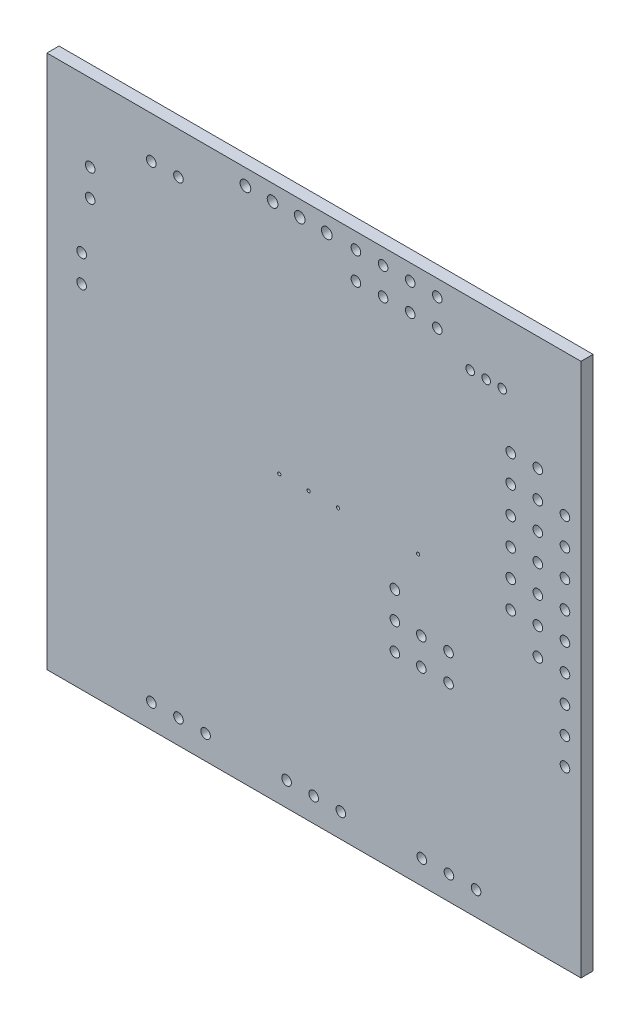
SolidWorks part; units mm, degrees
ref_plane "Спереди" through (0, 0, 0) normal (0, 0, 1) x (1, 0, 0)
ref_plane "Сверху" through (0, 0, 0) normal (0, 1, 0) x (1, 0, 0)
ref_plane "Справа" through (0, 0, 0) normal (1, 0, 0) x (0, 0, -1)
ref_plane "Плоскость1" through (0, 0, 1.1328) normal (0, 0, 1) x (1, 0, 0)
sketch "Эскиз1" plane through (0, 0, 1.1328) normal (0, 0, 1) x (1, 0, 0)
  line L0 (59.25, 11.75) -> (59.25, 61.75)
  line L1 (59.25, 61.75) -> (9.25, 61.75)
  line L2 (9.25, 61.75) -> (9.25, 11.75)
  line L3 (9.25, 11.75) -> (59.25, 11.75)
  circle A0 centre (57.75, 48.5) radius 0.45
  circle A1 centre (57.75, 45.95) radius 0.45
  circle A2 centre (55.21, 51.05) radius 0.45
  circle A3 centre (55.21, 48.5) radius 0.45
  circle A4 centre (55.21, 45.95) radius 0.45
  circle A5 centre (57.75, 43.4) radius 0.45
  circle A6 centre (52.67, 43.4) radius 0.45
  circle A7 centre (55.21, 43.4) radius 0.45
  circle A8 centre (50.375, 55.85) radius 0.4
  circle A9 centre (51.875, 55.85) radius 0.4
  circle A10 centre (45.8, 60.25) radius 0.45
  circle A11 centre (45.8, 57.71) radius 0.45
  circle A12 centre (52.67, 48.5) radius 0.45
  circle A13 centre (52.67, 45.95) radius 0.45
  circle A14 centre (48.875, 55.85) radius 0.4
  circle A15 centre (52.67, 51.05) radius 0.45
  circle A16 centre (57.75, 40.85) radius 0.45
  circle A17 centre (57.75, 38.3) radius 0.45
  circle A18 centre (55.21, 40.85) radius 0.45
  circle A19 centre (55.21, 38.3) radius 0.45
  circle A20 centre (57.75, 35.75) radius 0.45
  circle A21 centre (57.75, 33.2) radius 0.45
  circle A22 centre (57.75, 30.66) radius 0.45
  circle A23 centre (57.75, 28.12) radius 0.45
  circle A24 centre (52.67, 40.85) radius 0.45
  circle A25 centre (55.21, 35.75) radius 0.45
  circle A26 centre (52.67, 38.3) radius 0.45
  circle A27 centre (46.8501, 32.01) radius 0.45
  circle A28 centre (46.89, 14) radius 0.45
  circle A29 centre (49.43, 14) radius 0.45
  circle A30 centre (46.8501, 29.47) radius 0.45
  circle A31 centre (44.35, 14) radius 0.45
  circle A32 centre (40.72, 60.25) radius 0.45
  circle A33 centre (43.26, 60.25) radius 0.45
  circle A34 centre (32.915, 60.265) radius 0.5
  circle A35 centre (35.455, 60.265) radius 0.5
  circle A36 centre (40.72, 57.71) radius 0.45
  circle A37 centre (43.26, 57.71) radius 0.45
  circle A38 centre (38.18, 60.25) radius 0.45
  circle A39 centre (38.18, 57.71) radius 0.45
  circle A40 centre (27.835, 60.265) radius 0.5
  circle A41 centre (30.375, 60.265) radius 0.5
  circle A42 centre (19.025, 57.85) radius 0.45
  circle A43 centre (21.565, 57.85) radius 0.45
  circle A44 centre (13.3, 54.525) radius 0.45
  circle A45 centre (13.3, 51.985) radius 0.45
  circle A46 centre (12.5, 47.19) radius 0.45
  circle A47 centre (12.5, 44.65) radius 0.45
  circle A48 centre (44, 38.5) radius 0.15
  circle A49 centre (41.825, 34.55) radius 0.45
  circle A50 centre (36.5, 38.5) radius 0.15
  circle A51 centre (41.825, 32.01) radius 0.45
  circle A52 centre (44.3001, 32.01) radius 0.45
  circle A53 centre (44.3001, 29.47) radius 0.45
  circle A54 centre (41.825, 29.47) radius 0.45
  circle A55 centre (36.7675, 14) radius 0.45
  circle A56 centre (33.75, 38.5) radius 0.15
  circle A57 centre (34.2275, 14) radius 0.45
  circle A58 centre (31, 38.5) radius 0.15
  circle A59 centre (19.025, 14) radius 0.45
  circle A60 centre (24.105, 14) radius 0.45
  circle A61 centre (31.6875, 14) radius 0.45
  circle A62 centre (21.565, 14) radius 0.45
extrude "Бобышка-Вытянуть1" add sketch "Эскиз1" against normal blind 1.1328
